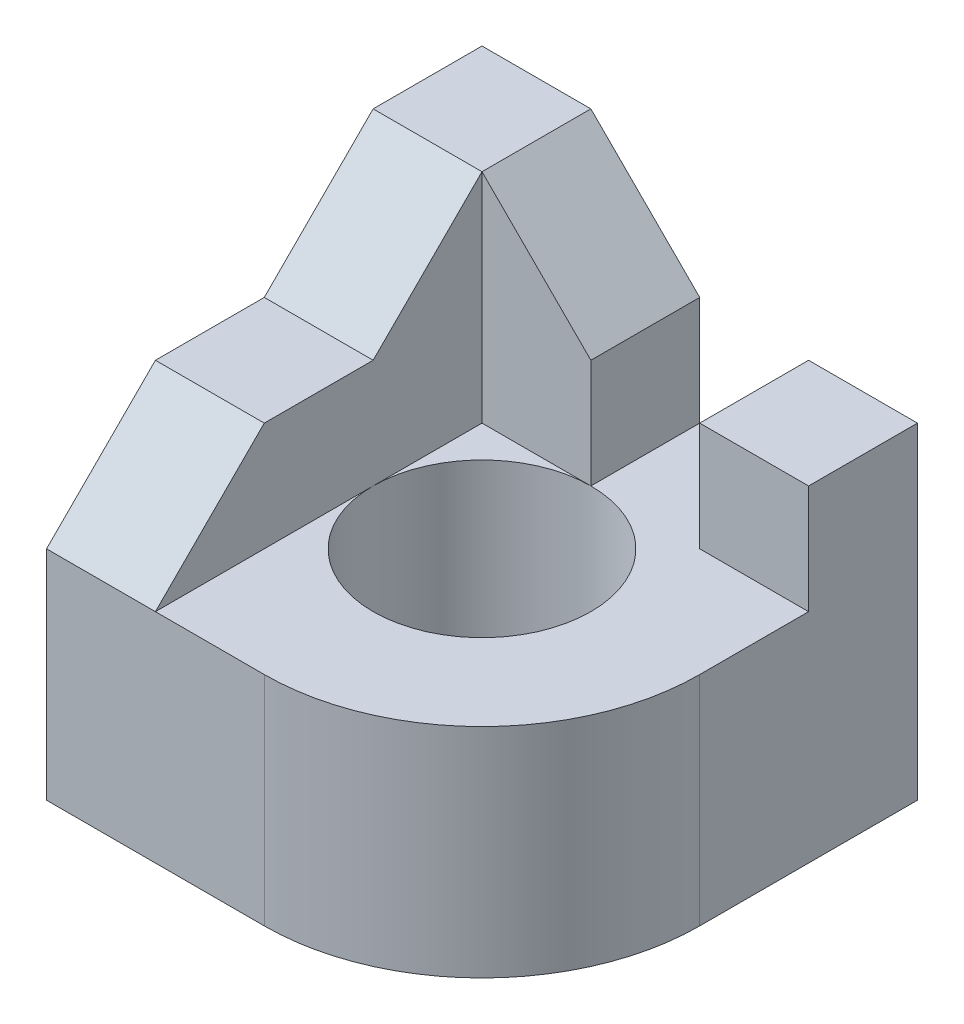
SolidWorks part; units mm, degrees
ref_plane "前基準面" through (0, 0, 0) normal (0, 0, 1) x (1, 0, 0)
ref_plane "上基準面" through (0, 0, 0) normal (0, 1, 0) x (1, 0, 0)
ref_plane "右基準面" through (0, 0, 0) normal (1, 0, 0) x (0, 0, -1)
sketch "草圖1" plane through (0, 0, 0) normal (0, 1, 0) x (1, 0, 0)
  line L1 (-20, -20) -> (20, -20)
  line L2 (-20, -20) -> (-20, 20)
  line L3 (-20, 20) -> (20, 20)
  line L4 (20, -20) -> (20, 20)
  line L5 (-20, -20) -> (20, 20) construction
  line L6 (-20, 20) -> (20, -20) construction
  point P0 (0, 0)
  dimension "D1" = 40
  dimension "D2" = 40
extrude "填料-伸長1" add sketch "草圖1" along normal blind 40
sketch "草圖2" plane through (0, 40, 0) normal (0, 1, 0) x (1, 0, 0)
  line L0 (20, -20) -> (20, 20) construction
  line L1 (-20, -20) -> (20, -20) construction
  line L6 (20, -20) -> (20, 20)
  line L7 (20, 20) -> (-20, 20)
  line L8 (-20, 20) -> (-20, -20)
  line L9 (-20, -20) -> (20, -20)
  line L10 (20, -20) -> (20, 20)
  line L11 (20, 20) -> (-20, 20)
  line L12 (-20, 20) -> (-20, -20)
  line L13 (-20, -20) -> (20, -20)
  circle A0 centre (0, 0) radius 10
  arc A1 (20, 0) -> (0, -20) centre (0, 0) cw
  line M5 (20, -20) -> (20, 20)
  dimension "D1" = 20
  dimension "D3" = 20
  dimension "D2" = 0
extrude "除料-伸長1" cut sketch "草圖2" against normal through all contours A0 | A1 L13 M5
sketch "草圖3" plane through (20, 0, 0) normal (1, 0, 0) x (0, 0, -1)
  line L0 (10, 40) -> (10, 20)
  line L1 (0, 40) -> (20, 40) construction
  line L2 (10, 20) -> (-20, 20)
  line L3 (-20, 0) -> (-20, 40) construction
  line L4 (20, 40) -> (20, 0) construction
  line L5 (10, 40) -> (-20, 40)
  line L6 (-20, 40) -> (-20, 20)
  dimension "D1" = 10
  dimension "D2" = 20
extrude "除料-伸長2" cut sketch "草圖3" against normal blind 20
sketch "草圖4" plane through (0, 0, 20) normal (0, 0, 1) x (1, 0, 0)
  line L0 (20, 30) -> (10, 30)
  line L1 (20, 20) -> (20, 40) construction
  line L2 (10, 30) -> (10, 20)
  line L3 (0, 20) -> (20, 20) construction
  line L4 (10, 20) -> (0, 20)
  line L5 (0, 20) -> (0, 30)
  line L6 (0, 40) -> (0, 20) construction
  line L7 (0, 30) -> (-10, 40)
  line L8 (-20, 40) -> (0, 40) construction
  line L9 (-10, 40) -> (20, 40)
  line L10 (20, 40) -> (20, 30)
  line L11 (-20, 40) -> (-20, 0) construction
  dimension "D1" = 10
  dimension "D2" = 10
  dimension "D3" = 10
extrude "除料-伸長3" cut sketch "草圖4" against normal through all
sketch "草圖5" plane through (20, 0, 0) normal (1, 0, 0) x (0, 0, -1)
  line L0 (10, 40) -> (0, 30)
  line L1 (20, 40) -> (0, 40) construction
  line L2 (0, 30) -> (-10, 30)
  line L3 (-10, 30) -> (-20, 20)
  line L4 (-20, 20) -> (-10, 20) construction
  line L5 (20, 40) -> (20, 30) construction
  line L6 (-20, 20) -> (-20, 40)
  line L7 (-20, 40) -> (10, 40)
  dimension "D1" = 10
  dimension "D2" = 10
  dimension "D3" = 10
  dimension "D4" = 10
extrude "除料-伸長4" cut sketch "草圖5" against normal through all
sketch "草圖7" plane through (0, 0, 20) normal (0, 0, 1) x (1, 0, 0)
  line L0 (-20, 20) -> (0, 20) construction
  line L1 (0, 30) -> (-10, 30)
  line L2 (0, 30) -> (0, 20)
  line L3 (0, 20) -> (-10, 20)
  line L4 (-10, 30) -> (-10, 20)
extrude "除料-伸長5" cut sketch "草圖7" against normal blind 20
sketch "草圖9" plane through (0, 20, 0) normal (0, 1, 0) x (1, 0, 0)
  line L1 (-10, 0) -> (-20, 0)
  line L2 (-10, 0) -> (-10, 10)
  line L3 (-10, 10) -> (-20, 10)
  line L4 (-20, 0) -> (-20, 10)
  line L5 (0, 10) -> (-10, 10)
  line L6 (0, 10) -> (0, 20)
  line L7 (0, 20) -> (-10, 20)
  line L8 (-10, 10) -> (-10, 20)
  arc A1 (0, 10) -> (-7.0711, 7.0711) centre (0, 0) ccw construction
  arc A2 (0, 10) -> (-7.0711, 7.0711) centre (0, 0) ccw
  arc A3 (-7.0711, 7.0711) -> (-10, 0) centre (0, 0) ccw construction
  arc A4 (-7.0711, 7.0711) -> (-10, 0) centre (0, 0) ccw
extrude "除料-伸長6" cut sketch "草圖9" along normal through all contours A4 A2 L5 L2
